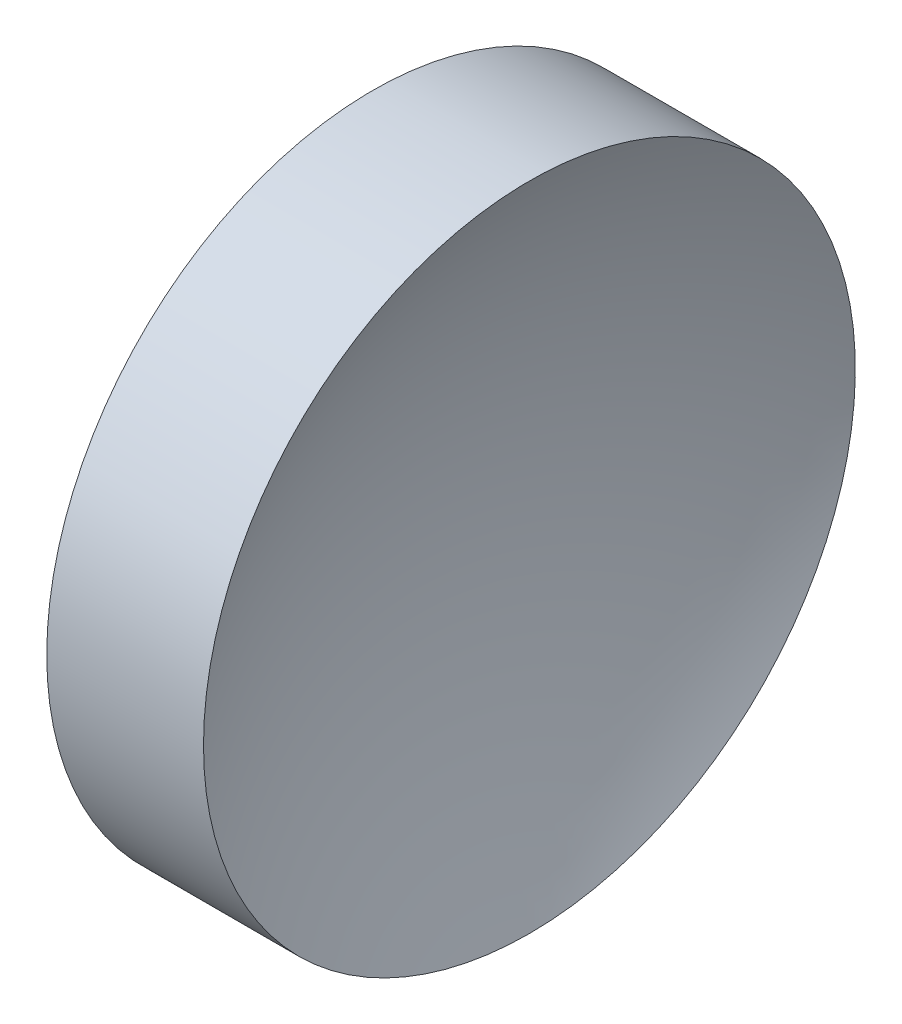
SolidWorks part; units mm, degrees
ref_plane "前视基准面" through (0, 0, 0) normal (0, 0, 1) x (1, 0, 0)
ref_plane "上视基准面" through (0, 0, 0) normal (0, 1, 0) x (1, 0, 0)
ref_plane "右视基准面" through (0, 0, 0) normal (1, 0, 0) x (0, 0, -1)
sketch "草图1" plane through (0, 0, 0) normal (0, 0, 1) x (1, 0, 0)
  line L0 (44.7821, 28.4776) -> (52.988, 28.4776) construction
  line L1 (47.7537, 28.4776) -> (47.7537, 34.8276)
  line L2 (47.7537, 34.8276) -> (50.8078, 34.8276)
  line L3 (49.2537, 28.4776) -> (47.7537, 28.4776)
  arc A0 (50.8078, 34.8276) -> (49.2537, 28.4776) centre (63.0037, 28.4776) ccw
revolve "旋转1" add sketch "草图1" angle 360 about L0
